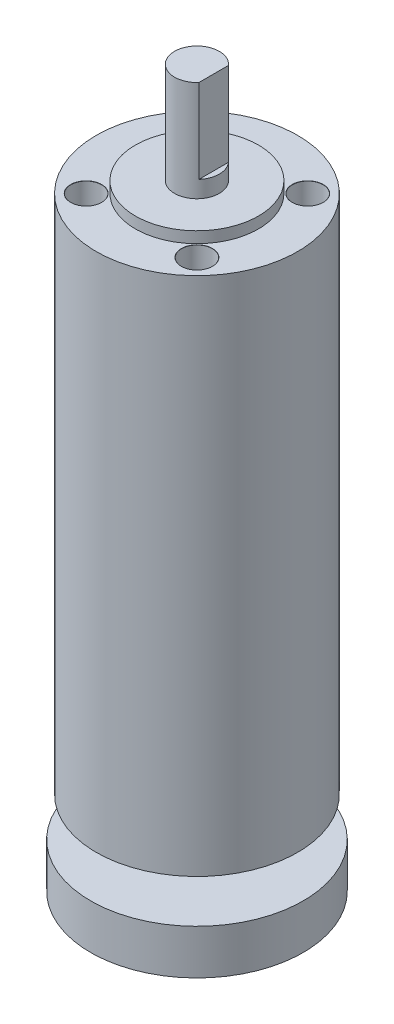
SolidWorks part; units mm, degrees
ref_plane "Front Plane" through (0, 0, 0) normal (0, 0, 1) x (1, 0, 0)
ref_plane "Top Plane" through (0, 0, 0) normal (0, 1, 0) x (1, 0, 0)
ref_plane "Right Plane" through (0, 0, 0) normal (1, 0, 0) x (0, 0, -1)
sketch "Sketch1" plane through (0, 0, 0) normal (0, 0, 1) x (1, 0, 0)
  line L4 (18, 93) -> (11, 93)
  line L5 (11, 93) -> (11, 95)
  line L6 (11, 95) -> (4, 95)
  line L7 (4, 95) -> (4, 113)
  line L8 (4, 113) -> (0, 113)
  line L9 (0, 113) -> (0, 0)
  line L12 (18, 93) -> (18, 57)
  line L13 (18, 57) -> (18, 0)
  line L14 (0, 0) -> (0, -15)
  line L15 (0, -15) -> (19, -15)
  line L16 (19, -15) -> (19, -7)
  line L17 (19, -7) -> (7, -7)
  line L18 (7, -7) -> (7, 0)
  line L19 (7, 0) -> (18, 0)
  dimension "D1" = 4
  dimension "D2" = 18
  dimension "D3" = 20
  dimension "D4" = 11
  dimension "D5" = 57
  dimension "D6" = 36
revolve "Revolve1" add sketch "Sketch1" angle 360 about L9
sketch "Sketch2" plane through (0, 0, 0) normal (0, 0, 1) x (1, 0, 0)
  line L0 (-4, 113) -> (3, 113)
  line L1 (4, 113) -> (-4, 113) construction
  line L2 (3, 113) -> (3, 98)
  line L3 (3, 98) -> (4.7045, 98)
  line L4 (4.7045, 98) -> (4.7045, 113)
  line L5 (4.7045, 113) -> (3, 113)
  dimension "D1" = 7
  dimension "D2" = 15
  dimension "D3" = 1.7045
extrude "Cut-Extrude1" cut sketch "Sketch2" against normal through all both and the other way through all contours L4 L5 L2 L3
hole_wizard "M5 Clearance Hole1" positions "Sketch5" profile "Sketch4" hole size "M5" standard "ANSI Metric"
sketch "Sketch5" plane through (0, 93, 0) normal (0, 1, 0) x (1, 0, 0)
  line L0 (0, 0) -> (-9.8995, 9.8995)
  line L2 (0, 0) -> (0, 1.4936)
  circle A0 centre (0, 0) radius 14
  point P0 (-9.8995, 9.8995)
  point P2 (-9.8995, -9.8995)
  point P4 (9.8995, -9.8995)
  point P6 (9.8995, 9.8995)
  dimension "D1" = 28
  dimension "D2" = 45
sketch "Sketch4" plane through (-9.8995, 93, -9.8995) normal (1, 0, 0) x (0, 0, 1)
  line L0 (0, 0) -> (0, 14.6524)
  line L1 (0, 14.6524) -> (2.75, 13)
  line L2 (2.75, 13) -> (2.75, 0.025)
  line L3 (2.75, 0.025) -> (2.775, 0)
  line L5 (2.775, 0) -> (0, 0)
  line L6 (-2.75, 0.025) -> (-2.775, 0) construction
  line L10 (0, 14.6524) -> (-2.75, 13) construction
  line L11 (0, -6.35) -> (0, 107.95) construction
  dimension "Hole Dia." = 5.5
  dimension "Hole Depth" = 13
  dimension "Near C'Sink Dia." = 5.55
  dimension "Near C'Sink Angle" = 90
  dimension "Drill Angle" = 118
